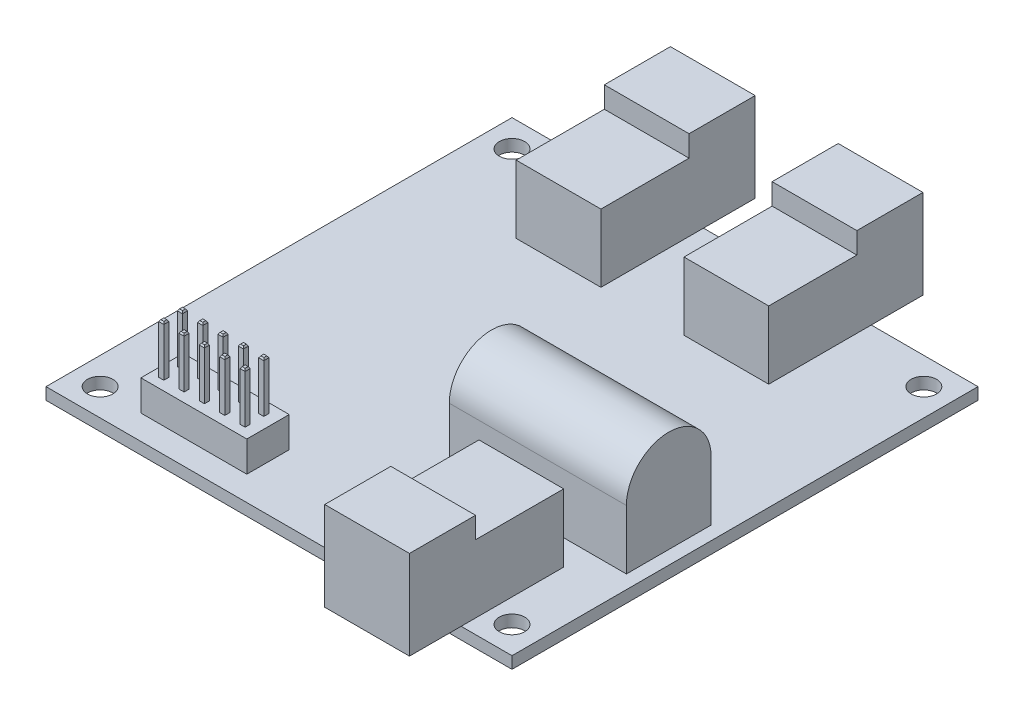
SolidWorks part; units mm, degrees
ref_plane "Front Plane" through (0, 0, 0) normal (0, 0, 1) x (1, 0, 0)
ref_plane "Top Plane" through (0, 0, 0) normal (0, 1, 0) x (1, 0, 0)
ref_plane "Right Plane" through (0, 0, 0) normal (1, 0, 0) x (0, 0, -1)
sketch "Sketch1" plane through (0, 0, 0) normal (0, 1, 0) x (1, 0, 0)
  line L0 (0, 54.99) -> (3.195, 51.795) construction
  line L1 (0, 0) -> (54.99, 0)
  line L2 (0, 0) -> (0, 54.99)
  line L3 (0, 54.99) -> (54.99, 54.99)
  line L4 (54.99, 0) -> (54.99, 54.99)
  line L5 (3.195, 51.795) -> (51.795, 51.795) construction
  line L6 (3.195, 51.795) -> (3.195, 3.195) construction
  line L7 (3.195, 3.195) -> (51.795, 3.195) construction
  line L8 (51.795, 51.795) -> (51.795, 3.195) construction
  line L9 (54.99, 54.99) -> (51.795, 51.795) construction
  line L10 (54.99, 0) -> (51.795, 3.195) construction
  circle A0 centre (3.195, 51.795) radius 1.5
  circle A1 centre (51.795, 51.795) radius 1.5
  circle A2 centre (3.195, 3.195) radius 1.5
  circle A3 centre (51.795, 3.195) radius 1.5
  dimension "D3" = 3
  dimension "D1" = 54.99
  dimension "D2" = 48.6
extrude "Boss-Extrude1" add sketch "Sketch1" along normal blind 1.4
sketch "Sketch2" plane through (0, 1.4, 0) normal (0, 1, 0) x (1, 0, 0)
  line L0 (0, 54.99) -> (12.595, 61.09) construction
  line L1 (12.595, 61.09) -> (22.595, 61.09)
  line L2 (12.595, 61.09) -> (12.595, 42.89)
  line L3 (12.595, 42.89) -> (22.595, 42.89)
  line L4 (22.595, 61.09) -> (22.595, 42.89)
  line L5 (32.395, 61.09) -> (42.395, 61.09)
  line L6 (32.395, 61.09) -> (32.395, 42.89)
  line L7 (32.395, 42.89) -> (42.395, 42.89)
  line L8 (42.395, 61.09) -> (42.395, 42.89)
  line L9 (42.395, 61.09) -> (54.99, 54.99) construction
  line L10 (54.99, 54.99) -> (0, 54.99) construction
  line L11 (54.99, 0) -> (54.99, 54.99) construction
  line L12 (38.99, 12.1) -> (48.99, 12.1)
  line L13 (38.99, 12.1) -> (38.99, -6.1)
  line L14 (38.99, -6.1) -> (48.99, -6.1)
  line L15 (48.99, 12.1) -> (48.99, -6.1)
  line L16 (0, 0) -> (54.99, 0) construction
  dimension "D1" = 10
  dimension "D2" = 9.8
  dimension "D3" = 18.2
  dimension "D4" = 6.1
  dimension "D5" = 6
  dimension "D6" = 6.1
extrude "Boss-Extrude2" add sketch "Sketch2" along normal blind 10.5
sketch "Sketch3" plane through (0, 11.9, 0) normal (0, 1, 0) x (1, 0, 0)
  line L0 (32.395, 61.09) -> (32.395, 42.89) construction
  line L1 (42.395, 42.89) -> (32.395, 42.89)
  line L2 (42.395, 42.89) -> (42.395, 53.29)
  line L3 (42.395, 53.29) -> (32.395, 53.29)
  line L4 (32.395, 42.89) -> (32.395, 53.29)
  line L5 (22.595, 42.89) -> (22.595, 61.09) construction
  line L6 (22.595, 53.29) -> (12.595, 53.29)
  line L7 (22.595, 53.29) -> (22.595, 42.89)
  line L8 (22.595, 42.89) -> (12.595, 42.89)
  line L9 (12.595, 53.29) -> (12.595, 42.89)
  line L10 (42.395, 61.09) -> (32.395, 61.09) construction
  line L11 (48.99, -6.1) -> (48.99, 12.1) construction
  line L12 (38.99, 12.1) -> (48.99, 12.1)
  line L13 (38.99, 12.1) -> (38.99, 1.7)
  line L14 (38.99, 1.7) -> (48.99, 1.7)
  line L15 (48.99, 12.1) -> (48.99, 1.7)
  dimension "D1" = 7.8
extrude "Cut-Extrude1" cut sketch "Sketch3" against normal offset from surface (2.5 mm away) 8 up to face at (51.795, 1.4, -1.695)
sketch "Sketch4" plane through (0, 1.4, 0) normal (0, 1, 0) x (1, 0, 0)
  line L0 (0, 54.99) -> (0, 0) construction
  line L1 (8.3, 7.9) -> (20.8, 7.9)
  line L2 (8.3, 7.9) -> (8.3, 2.9)
  line L3 (8.3, 2.9) -> (20.8, 2.9)
  line L4 (20.8, 7.9) -> (20.8, 2.9)
  line L5 (0, 0) -> (38.99, 0) construction
  dimension "D1" = 12.5
  dimension "D2" = 5
  dimension "D3" = 8.3
  dimension "D4" = 2.9
extrude "Boss-Extrude4" add sketch "Sketch4" along normal blind 3.6
sketch "Sketch5" plane through (0, 5, 0) normal (0, 1, 0) x (1, 0, 0)
  line L0 (8.3, 7.9) -> (9.3, 6.8) construction
  line L1 (9.3, 6.8) -> (9.9, 6.8)
  line L2 (9.3, 6.8) -> (9.3, 6.2)
  line L3 (9.3, 6.2) -> (9.9, 6.2)
  line L4 (9.9, 6.8) -> (9.9, 6.2)
  line L5 (9.3, 4.6) -> (9.9, 4.6)
  line L6 (9.3, 4.6) -> (9.3, 4)
  line L7 (9.3, 4) -> (9.9, 4)
  line L8 (9.9, 4.6) -> (9.9, 4)
  line L9 (9.3, 4) -> (8.3, 2.9) construction
  line L10 (8.3, 7.9) -> (8.3, 2.9) construction
  dimension "D1" = 0.6
  dimension "D2" = 1.6
  dimension "D3" = 1
extrude "Boss-Extrude5" add sketch "Sketch5" along normal blind 5.9
chamfer "Chamfer1" distance 0.2 angle 32 8 edges at (9.6, 10.9, -4.6) (9.9, 10.9, -4.3) (9.6, 10.9, -4) (9.3, 10.9, -4.3) (9.6, 10.9, -6.8) (9.9, 10.9, -6.5) (9.6, 10.9, -6.2) (9.3, 10.9, -6.5)
pattern_linear "LPattern1" count 5 spacing 2.4 along (1, 0, 0) of "Boss-Extrude5", "Chamfer1"
sketch "Sketch6" plane through (0, 1.4, 0) normal (0, 1, 0) x (1, 0, 0)
  line L0 (48.99, 12.1) -> (38.99, 12.1) construction
  line L1 (32.49, 25.1) -> (53.39, 25.1)
  line L2 (32.49, 25.1) -> (32.49, 15.1)
  line L3 (32.49, 15.1) -> (53.39, 15.1)
  line L4 (53.39, 25.1) -> (53.39, 15.1)
  line L5 (54.99, 0) -> (54.99, 54.99) construction
  dimension "D1" = 20.9
  dimension "D2" = 3
  dimension "D3" = 1.6
  dimension "D4" = 10
extrude "Boss-Extrude6" add sketch "Sketch6" along normal blind 12
sketch "Sketch7" plane through (53.39, 0, 0) normal (1, 0, 0) x (0, 0, -1)
  line L0 (15.1, 8.4) -> (15.1, 13.4)
  line L1 (15.1, 13.4) -> (15.1, 1.4) construction
  line L2 (15.1, 13.4) -> (25.1, 13.4)
  line L3 (25.1, 13.4) -> (25.1, 8.4)
  line L4 (25.1, 13.4) -> (25.1, 1.4) construction
  arc A0 (15.1, 8.4) -> (25.1, 8.4) centre (20.1, 8.4) cw
  line M2 (25.1, 1.4) -> (25.1, 13.4)
  line M3 (25.1, 13.4) -> (15.1, 13.4)
  line M4 (15.1, 13.4) -> (15.1, 1.4)
extrude "Cut-Extrude2" cut sketch "Sketch7" against normal through all contours A0 L2 M4 | A0 M3 M2
